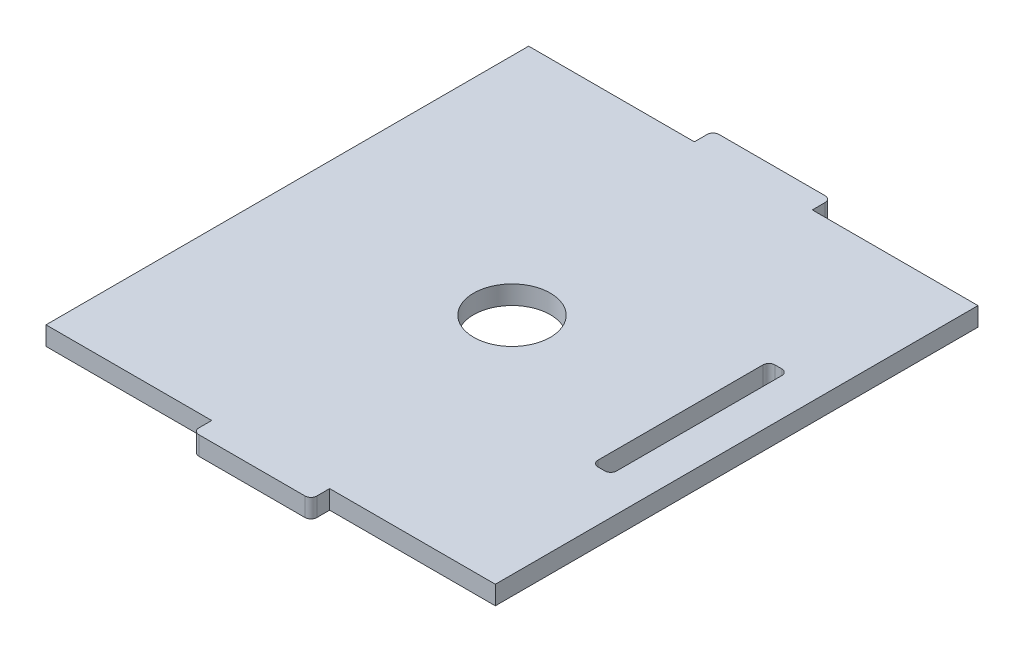
SolidWorks part; units mm, degrees
ref_plane "Front Plane" through (0, 0, 0) normal (0, 0, 1) x (1, 0, 0)
ref_plane "Top Plane" through (0, 0, 0) normal (0, 1, 0) x (1, 0, 0)
ref_plane "Right Plane" through (0, 0, 0) normal (1, 0, 0) x (0, 0, -1)
sketch "Sketch1" plane through (0, 0, 0) normal (0, 1, 0) x (1, 0, 0)
  line L0 (-10, 40.925) -> (10, 40.925) construction
  line L1 (-38.1, -40.925) -> (-10, -40.925)
  line L2 (-38.1, -40.925) -> (-38.1, 40.925)
  line L3 (-38.1, 40.925) -> (-10, 40.925)
  line L4 (38.1, -40.925) -> (38.1, 40.925)
  line L5 (-38.1, -40.925) -> (38.1, 40.925) construction
  line L6 (-38.1, 40.925) -> (38.1, -40.925) construction
  line L7 (-10, 40.925) -> (10, 40.925) construction
  line L8 (-10, 40.925) -> (-10, 44.1)
  line L9 (-10, 44.1) -> (10, 44.1)
  line L10 (10, 40.925) -> (10, 44.1)
  line L11 (10, 40.925) -> (38.1, 40.925)
  line L12 (0, 0) -> (-5.8133, 0) construction
  line L13 (10, -40.925) -> (10, -44.1)
  line L14 (-10, -44.1) -> (10, -44.1)
  line L15 (-10, -40.925) -> (-10, -44.1)
  line L16 (-10, -40.925) -> (10, -40.925) construction
  line L17 (10, -40.925) -> (38.1, -40.925)
  point P0 (0, 0)
  point P10 (-10, 42.5125)
  dimension "D1" = 76.2
  dimension "D2" = 81.85
  dimension "D3" = 20
  dimension "D4" = 3.175
extrude "Boss-Extrude1" add sketch "Sketch1" along normal blind 3.175
sketch "Sketch2" plane through (0, 3.175, 0) normal (0, 1, 0) x (1, 0, 0)
  line L0 (31.75, 40.925) -> (31.75, -40.925) construction
  line L1 (38.1, 40.925) -> (10, 40.925) construction
  line L2 (10, -40.925) -> (38.1, -40.925) construction
  line L3 (38.1, -40.925) -> (38.1, 40.925) construction
  line L4 (0, 0) -> (28.575, 0) construction
  line L5 (31.75, 0) -> (28.575, 0) construction
  line L6 (31.75, 15) -> (31.75, -15)
  line L7 (31.75, -15) -> (28.575, -15)
  line L8 (28.575, 15) -> (28.575, -15)
  line L9 (31.75, 15) -> (28.575, 15)
  line L10 (28.575, 0) -> (31.75, 0) construction
  line L11 (31.75, 0) -> (38.1, 0) construction
  circle A0 centre (0, 0) radius 6.5
  point P15 (30.1625, 0)
  dimension "D1" = 13
  dimension "D2" = 6.35
  dimension "D3" = 3.175
  dimension "D4" = 15
extrude "Cut-Extrude1" cut sketch "Sketch2" against normal through all
fillet "Fillet1" radius 1 8 edges at (28.575, 1.5875, -15) (31.75, 1.5875, -15) (28.575, 1.5875, 15) (31.75, 1.5875, 15) (10, 1.5875, 44.1) (-10, 1.5875, 44.1) (-10, 1.5875, -44.1) (10, 1.5875, -44.1)
